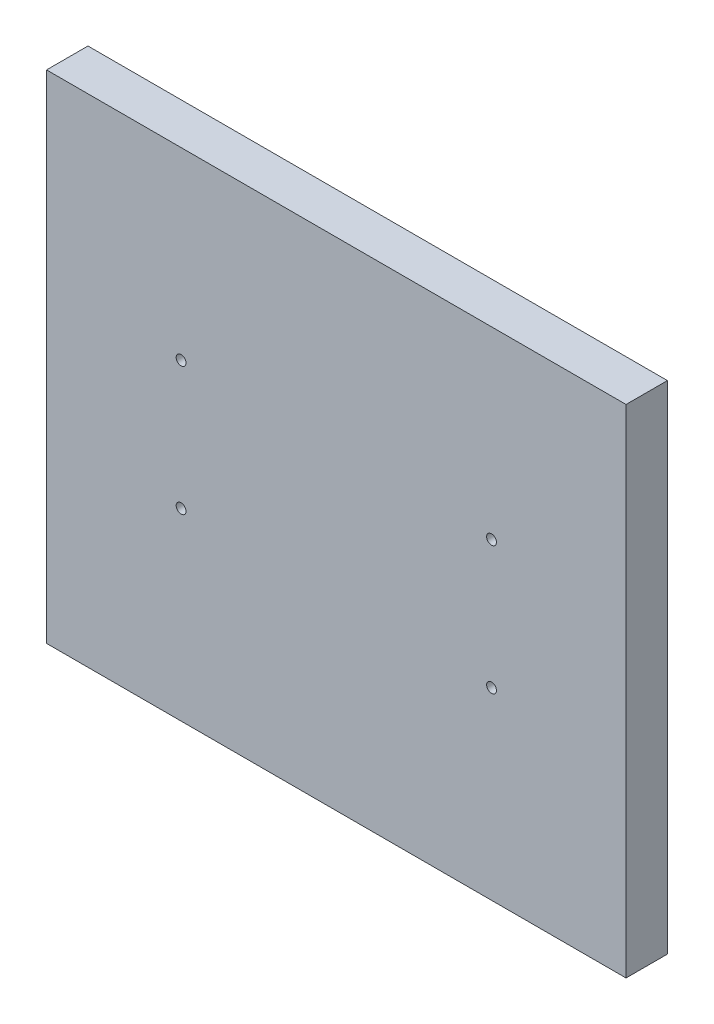
SolidWorks part; units mm, degrees
ref_plane "Ön Düzlem" through (0, 0, 0) normal (0, 0, 1) x (1, 0, 0)
ref_plane "Üst Düzlem" through (0, 0, 0) normal (0, 1, 0) x (1, 0, 0)
ref_plane "Sağ Düzlem" through (0, 0, 0) normal (1, 0, 0) x (0, 0, -1)
sketch "Sketch1" plane through (0, 0, 0) normal (0, 0, 1) x (1, 0, 0)
  line L1 (-70, 60) -> (70, 60)
  line L2 (-70, 60) -> (-70, -60)
  line L3 (-70, -60) -> (70, -60)
  line L4 (70, 60) -> (70, -60)
  line L5 (-70, 60) -> (70, -60) construction
  line L6 (-70, -60) -> (70, 60) construction
  point P0 (0, 0)
  dimension "D1" = 140
  dimension "D2" = 120
extrude "Boss-Extrude1" add sketch "Sketch1" along normal blind 10
hole_wizard "#4-48 Tapped Hole1" positions "Sketch3" profile "Sketch2" tap size "#4-48" standard "ANSI Inch"
sketch "Sketch3" plane through (0, 0, 10) normal (0, 0, 1) x (1, 0, 0)
  point P0 (-37.5, 15.5)
  point P3 (-37.5, -15.5)
  point P6 (37.5, 15.5)
  point P9 (37.5, -15.5)
sketch "Sketch2" plane through (-37.5, 15.5, 10) normal (1, 0, 0) x (0, -1, 0)
  line L0 (0, 0) -> (0, 7.9835)
  line L1 (0, 7.9835) -> (1.1874, 7.27)
  line L2 (1.1874, 7.27) -> (1.1874, 0)
  line L5 (1.1874, 0) -> (0, 0)
  line L10 (0, 7.9835) -> (-1.1875, 7.27) construction
  line L11 (0, -6.35) -> (0, 107.95) construction
  dimension "Tap Drill Dia." = 2.3749
  dimension "Tap Drill Depth" = 7.27
  dimension "Drill Angle" = 118
